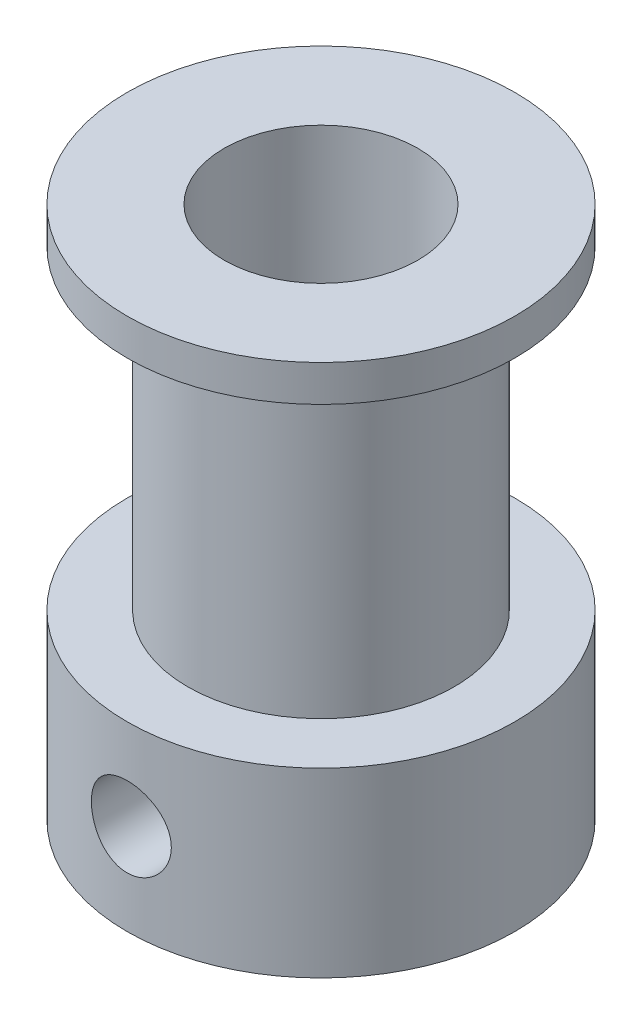
SolidWorks part; units mm, degrees
material "aluminio"
ref_plane "Alzado" through (0, 0, 0) normal (0, 0, 1) x (1, 0, 0)
ref_plane "Planta" through (0, 0, 0) normal (0, 1, 0) x (1, 0, 0)
ref_plane "Vista lateral" through (0, 0, 0) normal (1, 0, 0) x (0, 0, -1)
sketch "Croquis1" plane through (0, 0, 0) normal (0, 1, 0) x (1, 0, 0)
  circle A0 centre (0, 0) radius 8
  dimension "D1" = 16
extrude "Saliente-Extruir1" add sketch "Croquis1" along normal blind 7.5
sketch "Croquis2" plane through (0, 7.5, 0) normal (0, 1, 0) x (1, 0, 0)
  circle A0 centre (0, 0) radius 5.5
  dimension "D1" = 11
extrude "Saliente-Extruir2" add sketch "Croquis2" along normal blind 13
sketch "Croquis3" plane through (0, 20.5, 0) normal (0, 1, 0) x (1, 0, 0)
  circle A0 centre (0, 0) radius 8
  circle A1 centre (0, 0) radius 8 construction
extrude "Saliente-Extruir3" add sketch "Croquis3" along normal blind 1.5
sketch "Croquis4" plane through (0, 22, 0) normal (0, 1, 0) x (1, 0, 0)
  circle A0 centre (0, 0) radius 4
  dimension "D1" = 8
extrude "Cortar-Extruir1" cut sketch "Croquis4" against normal through all
sketch "Croquis5" plane through (0, 0, 0) normal (0, 0, 1) x (1, 0, 0)
  line L0 (0, 7.5) -> (0, 20.5)
  line L2 (-8, 20.5) -> (8, 20.5) construction
  line L3 (8, 7.5) -> (-8, 7.5) construction
  point P7 (0, 14)
hole_wizard "Taladro roscado M41 (falta definir posicio)" positions "Croquis7" profile "Croquis6" tap size "M4" standard "Iso"
sketch "Croquis7" plane through (0, 0, 0) normal (0, 0, 1) x (1, 0, 0)
  line L0 (0, 7.5) -> (0, 0) construction
  line L1 (8, 7.5) -> (-8, 7.5) construction
  point P7 (0, 3.75)
sketch "Croquis6" plane through (0, 3.75, 0) normal (1, 0, 0) x (0, 1, 0)
  line L0 (0, 0) -> (0, 8.001)
  line L1 (0, 8.001) -> (1.65, 8.001)
  line L2 (1.65, 8.001) -> (1.65, 0)
  line L5 (1.65, 0) -> (0, 0)
  line L11 (0, -6.35) -> (0, 107.95) construction
  dimension "Diámetro de perforador para roscar hasta el siguiente" = 3.3
  dimension "Profundidad de perforador para roscar hasta el siguiente" = 8.001
cosmetic thread "Rosca de taladro1" parameters "D2"=4
cosmetic thread "Rosca cosmética3" parameters "D2"=4
pattern_circular "MatrizC1" count 2 over 90 about axis through (0, 7.5, 0) along (0, -1, 0) of "Taladro roscado M41 (falta definir posicio)"
cosmetic thread "Rosca cosmética4" parameters "D2"=4
